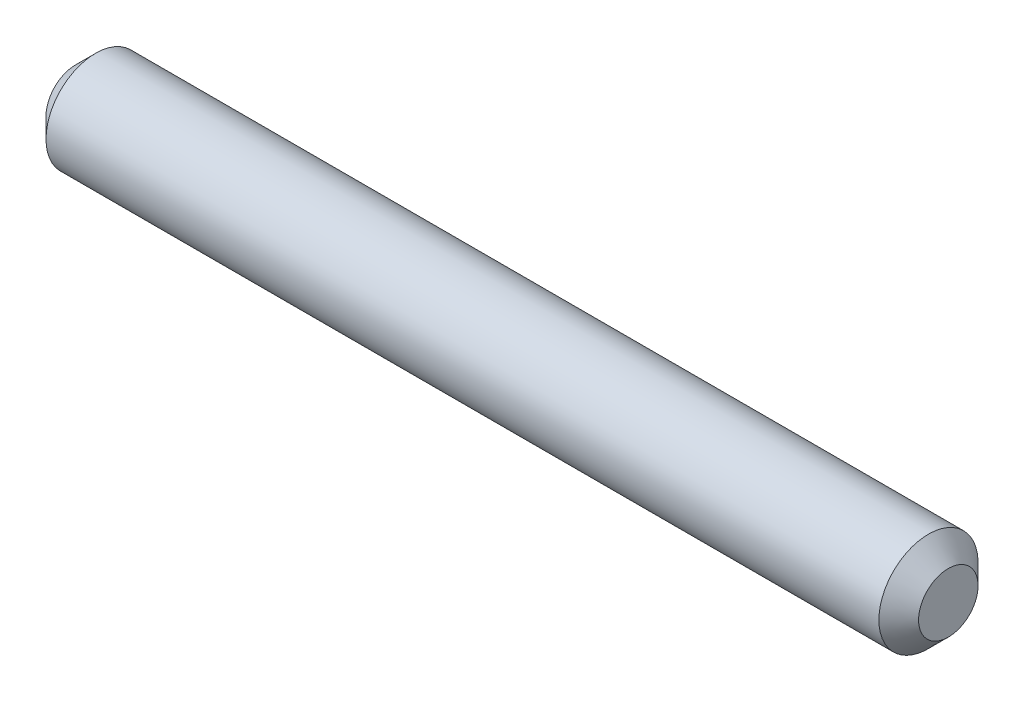
SolidWorks part; units mm, degrees
ref_plane "Płaszczyzna przednia" through (0, 0, 0) normal (0, 0, 1) x (1, 0, 0)
ref_plane "Płaszczyzna górna" through (0, 0, 0) normal (0, 1, 0) x (1, 0, 0)
ref_plane "Płaszczyzna prawa" through (0, 0, 0) normal (1, 0, 0) x (0, 0, -1)
sketch "Szkic1" plane through (0, 0, 0) normal (0, 0, 1) x (1, 0, 0)
  line L0 (0, 1.5) -> (1, 2.5)
  line L1 (0, 0) -> (44, 0)
  line L2 (0, 0) -> (0, 1.5)
  line L3 (1, 2.5) -> (43, 2.5)
  line L4 (44, 0) -> (44, 1.5)
  line L5 (43, 2.5) -> (44, 1.5)
  point P1 (44, 2.5)
  point P2 (0, 2.5)
  dimension "D1" = 44
  dimension "D2" = 2.5
revolve "Obrót1" add sketch "Szkic1" angle 360 about L1
